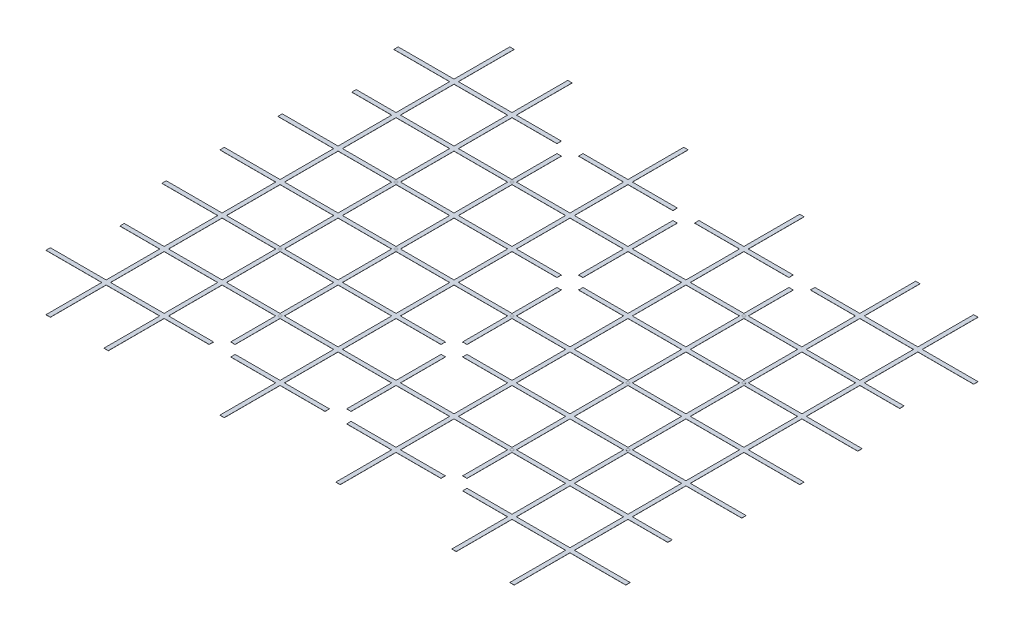
SolidWorks part; units mm, degrees
ref_plane "前视基准面" through (0, 0, 0) normal (0, 0, 1) x (1, 0, 0)
ref_plane "上视基准面" through (0, 0, 0) normal (0, 1, 0) x (1, 0, 0)
ref_plane "右视基准面" through (0, 0, 0) normal (1, 0, 0) x (0, 0, -1)
sketch "草图1" plane through (0, 0, 0) normal (0, 1, 0) x (1, 0, 0)
  line L1 (0, 0) -> (4000, 0)
  line L2 (0, 0) -> (0, 3200)
  line L3 (0, 3200) -> (4000, 3200)
  line L4 (4000, 0) -> (4000, 3200)
  dimension "D1" = 3200
  dimension "D2" = 4000
extrude "凸台-拉伸1" add sketch "草图1" along normal blind 1
sketch "草图2" plane through (0, 1, 0) normal (0, 1, 0) x (1, 0, 0)
  line L0 (0, 3200) -> (0, 0) construction
  line L1 (15, 15) -> (385, 15)
  line L2 (15, 15) -> (15, 385)
  line L3 (15, 385) -> (385, 385)
  line L4 (385, 15) -> (385, 385)
  line L5 (0, 0) -> (4000, 0) construction
  line L6 (200, 15) -> (200, 0) construction
  line L7 (415, 385) -> (785, 385)
  line L8 (415, 15) -> (415, 385)
  line L9 (415, 15) -> (785, 15)
  line L10 (785, 15) -> (785, 385)
  line L11 (815, 385) -> (1185, 385)
  line L12 (815, 15) -> (815, 385)
  line L13 (815, 15) -> (1185, 15)
  line L14 (1185, 15) -> (1185, 385)
  line L15 (1215, 385) -> (1585, 385)
  line L16 (1215, 15) -> (1215, 385)
  line L17 (1215, 15) -> (1585, 15)
  line L18 (1585, 15) -> (1585, 385)
  line L19 (1615, 385) -> (1985, 385)
  line L20 (1615, 15) -> (1615, 385)
  line L21 (1615, 15) -> (1985, 15)
  line L22 (1985, 15) -> (1985, 385)
  line L23 (2015, 385) -> (2385, 385)
  line L24 (2015, 15) -> (2015, 385)
  line L25 (2015, 15) -> (2385, 15)
  line L26 (2385, 15) -> (2385, 385)
  line L27 (2415, 385) -> (2785, 385)
  line L28 (2415, 15) -> (2415, 385)
  line L29 (2415, 15) -> (2785, 15)
  line L30 (2785, 15) -> (2785, 385)
  line L31 (2815, 385) -> (3185, 385)
  line L32 (2815, 15) -> (2815, 385)
  line L33 (2815, 15) -> (3185, 15)
  line L34 (3185, 15) -> (3185, 385)
  line L35 (3215, 385) -> (3585, 385)
  line L36 (3215, 15) -> (3215, 385)
  line L37 (3215, 15) -> (3585, 15)
  line L38 (3585, 15) -> (3585, 385)
  line L39 (3615, 385) -> (3985, 385)
  line L40 (3615, 15) -> (3615, 385)
  line L41 (3615, 15) -> (3985, 15)
  line L42 (3985, 15) -> (3985, 385)
  line L43 (415, 785) -> (785, 785)
  line L44 (415, 415) -> (415, 785)
  line L45 (415, 415) -> (785, 415)
  line L46 (785, 415) -> (785, 785)
  line L47 (815, 785) -> (1185, 785)
  line L48 (815, 415) -> (815, 785)
  line L49 (815, 415) -> (1185, 415)
  line L50 (1185, 415) -> (1185, 785)
  line L51 (1215, 785) -> (1585, 785)
  line L52 (1215, 415) -> (1215, 785)
  line L53 (1215, 415) -> (1585, 415)
  line L54 (1585, 415) -> (1585, 785)
  line L55 (1615, 785) -> (1985, 785)
  line L56 (1615, 415) -> (1615, 785)
  line L57 (1615, 415) -> (1985, 415)
  line L58 (1985, 415) -> (1985, 785)
  line L59 (2015, 785) -> (2385, 785)
  line L60 (2015, 415) -> (2015, 785)
  line L61 (2015, 415) -> (2385, 415)
  line L62 (2385, 415) -> (2385, 785)
  line L63 (2415, 785) -> (2785, 785)
  line L64 (2415, 415) -> (2415, 785)
  line L65 (2415, 415) -> (2785, 415)
  line L66 (2785, 415) -> (2785, 785)
  line L67 (2815, 785) -> (3185, 785)
  line L68 (2815, 415) -> (2815, 785)
  line L69 (2815, 415) -> (3185, 415)
  line L70 (3185, 415) -> (3185, 785)
  line L71 (3215, 785) -> (3585, 785)
  line L72 (3215, 415) -> (3215, 785)
  line L73 (3215, 415) -> (3585, 415)
  line L74 (3585, 415) -> (3585, 785)
  line L75 (3615, 785) -> (3985, 785)
  line L76 (3615, 415) -> (3615, 785)
  line L77 (3615, 415) -> (3985, 415)
  line L78 (3985, 415) -> (3985, 785)
  line L79 (415, 1185) -> (785, 1185)
  line L80 (415, 815) -> (415, 1185)
  line L81 (415, 815) -> (785, 815)
  line L82 (785, 815) -> (785, 1185)
  line L83 (815, 1185) -> (1185, 1185)
  line L84 (815, 815) -> (815, 1185)
  line L85 (815, 815) -> (1185, 815)
  line L86 (1185, 815) -> (1185, 1185)
  line L87 (1215, 1185) -> (1585, 1185)
  line L88 (1215, 815) -> (1215, 1185)
  line L89 (1215, 815) -> (1585, 815)
  line L90 (1585, 815) -> (1585, 1185)
  line L91 (1615, 1185) -> (1985, 1185)
  line L92 (1615, 815) -> (1615, 1185)
  line L93 (1615, 815) -> (1985, 815)
  line L94 (1985, 815) -> (1985, 1185)
  line L95 (2015, 1185) -> (2385, 1185)
  line L96 (2015, 815) -> (2015, 1185)
  line L97 (2015, 815) -> (2385, 815)
  line L98 (2385, 815) -> (2385, 1185)
  line L99 (2415, 1185) -> (2785, 1185)
  line L100 (2415, 815) -> (2415, 1185)
  line L101 (2415, 815) -> (2785, 815)
  line L102 (2785, 815) -> (2785, 1185)
  line L103 (2815, 1185) -> (3185, 1185)
  line L104 (2815, 815) -> (2815, 1185)
  line L105 (2815, 815) -> (3185, 815)
  line L106 (3185, 815) -> (3185, 1185)
  line L107 (3215, 1185) -> (3585, 1185)
  line L108 (3215, 815) -> (3215, 1185)
  line L109 (3215, 815) -> (3585, 815)
  line L110 (3585, 815) -> (3585, 1185)
  line L111 (3615, 1185) -> (3985, 1185)
  line L112 (3615, 815) -> (3615, 1185)
  line L113 (3615, 815) -> (3985, 815)
  line L114 (3985, 815) -> (3985, 1185)
  line L115 (415, 1585) -> (785, 1585)
  line L116 (415, 1215) -> (415, 1585)
  line L117 (415, 1215) -> (785, 1215)
  line L118 (785, 1215) -> (785, 1585)
  line L119 (815, 1585) -> (1185, 1585)
  line L120 (815, 1215) -> (815, 1585)
  line L121 (815, 1215) -> (1185, 1215)
  line L122 (1185, 1215) -> (1185, 1585)
  line L123 (1215, 1585) -> (1585, 1585)
  line L124 (1215, 1215) -> (1215, 1585)
  line L125 (1215, 1215) -> (1585, 1215)
  line L126 (1585, 1215) -> (1585, 1585)
  line L127 (1615, 1585) -> (1985, 1585)
  line L128 (1615, 1215) -> (1615, 1585)
  line L129 (1615, 1215) -> (1985, 1215)
  line L130 (1985, 1215) -> (1985, 1585)
  line L131 (2015, 1585) -> (2385, 1585)
  line L132 (2015, 1215) -> (2015, 1585)
  line L133 (2015, 1215) -> (2385, 1215)
  line L134 (2385, 1215) -> (2385, 1585)
  line L135 (2415, 1585) -> (2785, 1585)
  line L136 (2415, 1215) -> (2415, 1585)
  line L137 (2415, 1215) -> (2785, 1215)
  line L138 (2785, 1215) -> (2785, 1585)
  line L139 (2815, 1585) -> (3185, 1585)
  line L140 (2815, 1215) -> (2815, 1585)
  line L141 (2815, 1215) -> (3185, 1215)
  line L142 (3185, 1215) -> (3185, 1585)
  line L143 (3215, 1585) -> (3585, 1585)
  line L144 (3215, 1215) -> (3215, 1585)
  line L145 (3215, 1215) -> (3585, 1215)
  line L146 (3585, 1215) -> (3585, 1585)
  line L147 (3615, 1585) -> (3985, 1585)
  line L148 (3615, 1215) -> (3615, 1585)
  line L149 (3615, 1215) -> (3985, 1215)
  line L150 (3985, 1215) -> (3985, 1585)
  line L151 (415, 1985) -> (785, 1985)
  line L152 (415, 1615) -> (415, 1985)
  line L153 (415, 1615) -> (785, 1615)
  line L154 (785, 1615) -> (785, 1985)
  line L155 (815, 1985) -> (1185, 1985)
  line L156 (815, 1615) -> (815, 1985)
  line L157 (815, 1615) -> (1185, 1615)
  line L158 (1185, 1615) -> (1185, 1985)
  line L159 (1215, 1985) -> (1585, 1985)
  line L160 (1215, 1615) -> (1215, 1985)
  line L161 (1215, 1615) -> (1585, 1615)
  line L162 (1585, 1615) -> (1585, 1985)
  line L163 (1615, 1985) -> (1985, 1985)
  line L164 (1615, 1615) -> (1615, 1985)
  line L165 (1615, 1615) -> (1985, 1615)
  line L166 (1985, 1615) -> (1985, 1985)
  line L167 (2015, 1985) -> (2385, 1985)
  line L168 (2015, 1615) -> (2015, 1985)
  line L169 (2015, 1615) -> (2385, 1615)
  line L170 (2385, 1615) -> (2385, 1985)
  line L171 (2415, 1985) -> (2785, 1985)
  line L172 (2415, 1615) -> (2415, 1985)
  line L173 (2415, 1615) -> (2785, 1615)
  line L174 (2785, 1615) -> (2785, 1985)
  line L175 (2815, 1985) -> (3185, 1985)
  line L176 (2815, 1615) -> (2815, 1985)
  line L177 (2815, 1615) -> (3185, 1615)
  line L178 (3185, 1615) -> (3185, 1985)
  line L179 (3215, 1985) -> (3585, 1985)
  line L180 (3215, 1615) -> (3215, 1985)
  line L181 (3215, 1615) -> (3585, 1615)
  line L182 (3585, 1615) -> (3585, 1985)
  line L183 (3615, 1985) -> (3985, 1985)
  line L184 (3615, 1615) -> (3615, 1985)
  line L185 (3615, 1615) -> (3985, 1615)
  line L186 (3985, 1615) -> (3985, 1985)
  line L187 (415, 2385) -> (785, 2385)
  line L188 (415, 2015) -> (415, 2385)
  line L189 (415, 2015) -> (785, 2015)
  line L190 (785, 2015) -> (785, 2385)
  line L191 (815, 2385) -> (1185, 2385)
  line L192 (815, 2015) -> (815, 2385)
  line L193 (815, 2015) -> (1185, 2015)
  line L194 (1185, 2015) -> (1185, 2385)
  line L195 (1215, 2385) -> (1585, 2385)
  line L196 (1215, 2015) -> (1215, 2385)
  line L197 (1215, 2015) -> (1585, 2015)
  line L198 (1585, 2015) -> (1585, 2385)
  line L199 (1615, 2385) -> (1985, 2385)
  line L200 (1615, 2015) -> (1615, 2385)
  line L201 (1615, 2015) -> (1985, 2015)
  line L202 (1985, 2015) -> (1985, 2385)
  line L203 (2015, 2385) -> (2385, 2385)
  line L204 (2015, 2015) -> (2015, 2385)
  line L205 (2015, 2015) -> (2385, 2015)
  line L206 (2385, 2015) -> (2385, 2385)
  line L207 (2415, 2385) -> (2785, 2385)
  line L208 (2415, 2015) -> (2415, 2385)
  line L209 (2415, 2015) -> (2785, 2015)
  line L210 (2785, 2015) -> (2785, 2385)
  line L211 (2815, 2385) -> (3185, 2385)
  line L212 (2815, 2015) -> (2815, 2385)
  line L213 (2815, 2015) -> (3185, 2015)
  line L214 (3185, 2015) -> (3185, 2385)
  line L215 (3215, 2385) -> (3585, 2385)
  line L216 (3215, 2015) -> (3215, 2385)
  line L217 (3215, 2015) -> (3585, 2015)
  line L218 (3585, 2015) -> (3585, 2385)
  line L219 (3615, 2385) -> (3985, 2385)
  line L220 (3615, 2015) -> (3615, 2385)
  line L221 (3615, 2015) -> (3985, 2015)
  line L222 (3985, 2015) -> (3985, 2385)
  line L223 (415, 2785) -> (785, 2785)
  line L224 (415, 2415) -> (415, 2785)
  line L225 (415, 2415) -> (785, 2415)
  line L226 (785, 2415) -> (785, 2785)
  line L227 (815, 2785) -> (1185, 2785)
  line L228 (815, 2415) -> (815, 2785)
  line L229 (815, 2415) -> (1185, 2415)
  line L230 (1185, 2415) -> (1185, 2785)
  line L231 (1215, 2785) -> (1585, 2785)
  line L232 (1215, 2415) -> (1215, 2785)
  line L233 (1215, 2415) -> (1585, 2415)
  line L234 (1585, 2415) -> (1585, 2785)
  line L235 (1615, 2785) -> (1985, 2785)
  line L236 (1615, 2415) -> (1615, 2785)
  line L237 (1615, 2415) -> (1985, 2415)
  line L238 (1985, 2415) -> (1985, 2785)
  line L239 (2015, 2785) -> (2385, 2785)
  line L240 (2015, 2415) -> (2015, 2785)
  line L241 (2015, 2415) -> (2385, 2415)
  line L242 (2385, 2415) -> (2385, 2785)
  line L243 (2415, 2785) -> (2785, 2785)
  line L244 (2415, 2415) -> (2415, 2785)
  line L245 (2415, 2415) -> (2785, 2415)
  line L246 (2785, 2415) -> (2785, 2785)
  line L247 (2815, 2785) -> (3185, 2785)
  line L248 (2815, 2415) -> (2815, 2785)
  line L249 (2815, 2415) -> (3185, 2415)
  line L250 (3185, 2415) -> (3185, 2785)
  line L251 (3215, 2785) -> (3585, 2785)
  line L252 (3215, 2415) -> (3215, 2785)
  line L253 (3215, 2415) -> (3585, 2415)
  line L254 (3585, 2415) -> (3585, 2785)
  line L255 (3615, 2785) -> (3985, 2785)
  line L256 (3615, 2415) -> (3615, 2785)
  line L257 (3615, 2415) -> (3985, 2415)
  line L258 (3985, 2415) -> (3985, 2785)
  line L259 (415, 3185) -> (785, 3185)
  line L260 (415, 2815) -> (415, 3185)
  line L261 (415, 2815) -> (785, 2815)
  line L262 (785, 2815) -> (785, 3185)
  line L263 (815, 3185) -> (1185, 3185)
  line L264 (815, 2815) -> (815, 3185)
  line L265 (815, 2815) -> (1185, 2815)
  line L266 (1185, 2815) -> (1185, 3185)
  line L267 (1215, 3185) -> (1585, 3185)
  line L268 (1215, 2815) -> (1215, 3185)
  line L269 (1215, 2815) -> (1585, 2815)
  line L270 (1585, 2815) -> (1585, 3185)
  line L271 (1615, 3185) -> (1985, 3185)
  line L272 (1615, 2815) -> (1615, 3185)
  line L273 (1615, 2815) -> (1985, 2815)
  line L274 (1985, 2815) -> (1985, 3185)
  line L275 (2015, 3185) -> (2385, 3185)
  line L276 (2015, 2815) -> (2015, 3185)
  line L277 (2015, 2815) -> (2385, 2815)
  line L278 (2385, 2815) -> (2385, 3185)
  line L279 (2415, 3185) -> (2785, 3185)
  line L280 (2415, 2815) -> (2415, 3185)
  line L281 (2415, 2815) -> (2785, 2815)
  line L282 (2785, 2815) -> (2785, 3185)
  line L283 (2815, 3185) -> (3185, 3185)
  line L284 (2815, 2815) -> (2815, 3185)
  line L285 (2815, 2815) -> (3185, 2815)
  line L286 (3185, 2815) -> (3185, 3185)
  line L287 (3215, 3185) -> (3585, 3185)
  line L288 (3215, 2815) -> (3215, 3185)
  line L289 (3215, 2815) -> (3585, 2815)
  line L290 (3585, 2815) -> (3585, 3185)
  line L291 (3615, 3185) -> (3985, 3185)
  line L292 (3615, 2815) -> (3615, 3185)
  line L293 (3615, 2815) -> (3985, 2815)
  line L294 (3985, 2815) -> (3985, 3185)
  line L295 (15, 785) -> (385, 785)
  line L296 (15, 415) -> (15, 785)
  line L297 (15, 415) -> (385, 415)
  line L298 (385, 415) -> (385, 785)
  line L299 (15, 1185) -> (385, 1185)
  line L300 (15, 815) -> (15, 1185)
  line L301 (15, 815) -> (385, 815)
  line L302 (385, 815) -> (385, 1185)
  line L303 (15, 1585) -> (385, 1585)
  line L304 (15, 1215) -> (15, 1585)
  line L305 (15, 1215) -> (385, 1215)
  line L306 (385, 1215) -> (385, 1585)
  line L307 (15, 1985) -> (385, 1985)
  line L308 (15, 1615) -> (15, 1985)
  line L309 (15, 1615) -> (385, 1615)
  line L310 (385, 1615) -> (385, 1985)
  line L311 (15, 2385) -> (385, 2385)
  line L312 (15, 2015) -> (15, 2385)
  line L313 (15, 2015) -> (385, 2015)
  line L314 (385, 2015) -> (385, 2385)
  line L315 (15, 2785) -> (385, 2785)
  line L316 (15, 2415) -> (15, 2785)
  line L317 (15, 2415) -> (385, 2415)
  line L318 (385, 2415) -> (385, 2785)
  line L319 (15, 3185) -> (385, 3185)
  line L320 (15, 2815) -> (15, 3185)
  line L321 (15, 2815) -> (385, 2815)
  line L322 (385, 2815) -> (385, 3185)
  dimension "D1" = 15
  dimension "D2" = 15
  dimension "D3" = 200
  dimension "D4" = 10
  dimension "D5" = 8
extrude "切除-拉伸2" cut sketch "草图2" against normal through all
sketch "草图4" plane through (0, 1, 0) normal (0, 1, 0) x (1, 0, 0)
  line L1 (0, 3200) -> (385, 3200)
  line L2 (0, 3200) -> (0, 2815)
  line L3 (0, 2815) -> (385, 2815)
  line L4 (385, 3200) -> (385, 2815)
  line L5 (4000, 3200) -> (3615, 3200)
  line L6 (4000, 3200) -> (4000, 2815)
  line L7 (4000, 2815) -> (3615, 2815)
  line L8 (3615, 3200) -> (3615, 2815)
  line L9 (4000, 0) -> (3615, 0)
  line L10 (4000, 0) -> (4000, 385)
  line L11 (4000, 385) -> (3615, 385)
  line L12 (3615, 0) -> (3615, 385)
  line L13 (0, 0) -> (385, 0)
  line L14 (0, 0) -> (0, 385)
  line L15 (0, 385) -> (385, 385)
  line L16 (385, 0) -> (385, 385)
extrude "切除-拉伸4" cut sketch "草图4" against normal through all
sketch "草图5" plane through (0, 1, 0) normal (0, 1, 0) x (1, 0, 0)
  line L0 (385, 0) -> (3615, 0) construction
  line L1 (415, 15) -> (785, 15)
  line L2 (415, 15) -> (415, 0)
  line L3 (415, 0) -> (785, 0)
  line L4 (785, 15) -> (785, 0)
  line L5 (815, 15) -> (815, 0)
  line L6 (815, 15) -> (1185, 15)
  line L7 (815, 0) -> (1185, 0)
  line L8 (1185, 15) -> (1185, 0)
  line L9 (1215, 15) -> (1215, 0)
  line L10 (1215, 15) -> (1585, 15)
  line L11 (1215, 0) -> (1585, 0)
  line L12 (1585, 15) -> (1585, 0)
  line L13 (1615, 15) -> (1615, 0)
  line L14 (1615, 15) -> (1985, 15)
  line L15 (1615, 0) -> (1985, 0)
  line L16 (1985, 15) -> (1985, 0)
  line L17 (2015, 15) -> (2015, 0)
  line L18 (2015, 15) -> (2385, 15)
  line L19 (2015, 0) -> (2385, 0)
  line L20 (2385, 15) -> (2385, 0)
  line L21 (2415, 15) -> (2415, 0)
  line L22 (2415, 15) -> (2785, 15)
  line L23 (2415, 0) -> (2785, 0)
  line L24 (2785, 15) -> (2785, 0)
  line L25 (2815, 15) -> (2815, 0)
  line L26 (2815, 15) -> (3185, 15)
  line L27 (2815, 0) -> (3185, 0)
  line L28 (3185, 15) -> (3185, 0)
  line L29 (3215, 15) -> (3215, 0)
  line L30 (3215, 15) -> (3585, 15)
  line L31 (3215, 0) -> (3585, 0)
  line L32 (3585, 15) -> (3585, 0)
  line L33 (815, 3200) -> (815, 3185)
  line L34 (815, 3200) -> (1185, 3200)
  line L35 (815, 3185) -> (1185, 3185)
  line L36 (1185, 3200) -> (1185, 3185)
  line L37 (1215, 3200) -> (1215, 3185)
  line L38 (1215, 3200) -> (1585, 3200)
  line L39 (1215, 3185) -> (1585, 3185)
  line L40 (1585, 3200) -> (1585, 3185)
  line L41 (1615, 3200) -> (1615, 3185)
  line L42 (1615, 3200) -> (1985, 3200)
  line L43 (1615, 3185) -> (1985, 3185)
  line L44 (1985, 3200) -> (1985, 3185)
  line L45 (2015, 3200) -> (2015, 3185)
  line L46 (2015, 3200) -> (2385, 3200)
  line L47 (2015, 3185) -> (2385, 3185)
  line L48 (2385, 3200) -> (2385, 3185)
  line L49 (2415, 3200) -> (2415, 3185)
  line L50 (2415, 3200) -> (2785, 3200)
  line L51 (2415, 3185) -> (2785, 3185)
  line L52 (2785, 3200) -> (2785, 3185)
  line L53 (2815, 3200) -> (2815, 3185)
  line L54 (2815, 3200) -> (3185, 3200)
  line L55 (2815, 3185) -> (3185, 3185)
  line L56 (3185, 3200) -> (3185, 3185)
  line L57 (3215, 3200) -> (3215, 3185)
  line L58 (3215, 3200) -> (3585, 3200)
  line L59 (3215, 3185) -> (3585, 3185)
  line L60 (3585, 3200) -> (3585, 3185)
  line L61 (415, 3200) -> (415, 3185)
  line L62 (415, 3200) -> (785, 3200)
  line L63 (415, 3185) -> (785, 3185)
  line L64 (785, 3200) -> (785, 3185)
  line L65 (0, 2815) -> (0, 385) construction
  line L66 (15, 415) -> (0, 415)
  line L67 (15, 415) -> (15, 785)
  line L68 (15, 785) -> (0, 785)
  line L69 (0, 415) -> (0, 785)
  line L70 (385, 785) -> (15, 785) construction
  line L71 (4000, 785) -> (3985, 785)
  line L72 (3985, 415) -> (3985, 785)
  line L73 (4000, 415) -> (4000, 785)
  line L74 (4000, 415) -> (3985, 415)
  line L75 (4000, 1185) -> (3985, 1185)
  line L76 (3985, 815) -> (3985, 1185)
  line L77 (4000, 815) -> (4000, 1185)
  line L78 (4000, 815) -> (3985, 815)
  line L79 (4000, 1585) -> (3985, 1585)
  line L80 (3985, 1215) -> (3985, 1585)
  line L81 (4000, 1215) -> (4000, 1585)
  line L82 (4000, 1215) -> (3985, 1215)
  line L83 (4000, 1985) -> (3985, 1985)
  line L84 (3985, 1615) -> (3985, 1985)
  line L85 (4000, 1615) -> (4000, 1985)
  line L86 (4000, 1615) -> (3985, 1615)
  line L87 (4000, 2385) -> (3985, 2385)
  line L88 (3985, 2015) -> (3985, 2385)
  line L89 (4000, 2015) -> (4000, 2385)
  line L90 (4000, 2015) -> (3985, 2015)
  line L91 (4000, 2785) -> (3985, 2785)
  line L92 (3985, 2415) -> (3985, 2785)
  line L93 (4000, 2415) -> (4000, 2785)
  line L94 (4000, 2415) -> (3985, 2415)
  line L95 (15, 1185) -> (0, 1185)
  line L96 (0, 815) -> (0, 1185)
  line L97 (15, 815) -> (15, 1185)
  line L98 (15, 815) -> (0, 815)
  line L99 (15, 1585) -> (0, 1585)
  line L100 (0, 1215) -> (0, 1585)
  line L101 (15, 1215) -> (15, 1585)
  line L102 (15, 1215) -> (0, 1215)
  line L103 (15, 1985) -> (0, 1985)
  line L104 (0, 1615) -> (0, 1985)
  line L105 (15, 1615) -> (15, 1985)
  line L106 (15, 1615) -> (0, 1615)
  line L107 (15, 2385) -> (0, 2385)
  line L108 (0, 2015) -> (0, 2385)
  line L109 (15, 2015) -> (15, 2385)
  line L110 (15, 2015) -> (0, 2015)
  line L111 (15, 2785) -> (0, 2785)
  line L112 (0, 2415) -> (0, 2785)
  line L113 (15, 2415) -> (15, 2785)
  line L114 (15, 2415) -> (0, 2415)
  dimension "D1" = 8
  dimension "D2" = 2
  dimension "D3" = 2
  dimension "D4" = 6
extrude "切除-拉伸5" cut sketch "草图5" against normal through all
sketch "草图6" plane through (0, 1, 0) normal (0, 1, 0) x (1, 0, 0)
  line L0 (385, 2385) -> (0, 2385) construction
  line L1 (0, 2415) -> (110, 2415)
  line L2 (0, 2415) -> (0, 2385)
  line L3 (0, 2385) -> (110, 2385)
  line L4 (110, 2415) -> (110, 2385)
  line L5 (0, 815) -> (385, 815) construction
  line L6 (0, 785) -> (110, 785)
  line L7 (0, 785) -> (0, 815)
  line L8 (0, 815) -> (110, 815)
  line L9 (110, 785) -> (110, 815)
  line L10 (4000, 785) -> (3615, 785) construction
  line L11 (4000, 815) -> (3890, 815)
  line L12 (4000, 815) -> (4000, 785)
  line L13 (4000, 785) -> (3890, 785)
  line L14 (3890, 815) -> (3890, 785)
  line L15 (4000, 2385) -> (3615, 2385) construction
  line L16 (4000, 2415) -> (3890, 2415)
  line L17 (4000, 2415) -> (4000, 2385)
  line L18 (4000, 2385) -> (3890, 2385)
  line L19 (3890, 2415) -> (3890, 2385)
  line L20 (1200, 3200) -> (1200, 2800) construction
  line L21 (1215, 3200) -> (1185, 3200) construction
  line L23 (1125, 3200) -> (1275, 3200)
  line L24 (1125, 3200) -> (1125, 2800)
  line L25 (1125, 2800) -> (1275, 2800) construction
  line L26 (1275, 3200) -> (1275, 2800)
  line L27 (2000, 3200) -> (2000, 2800) construction
  line L28 (1925, 3200) -> (2075, 3200)
  line L29 (1925, 3200) -> (1925, 2800)
  line L30 (1925, 2800) -> (2075, 2800) construction
  line L31 (2075, 3200) -> (2075, 2800)
  line L32 (2015, 3200) -> (1985, 3200) construction
  line L33 (2800, 3200) -> (2800, 2800) construction
  line L34 (2725, 3200) -> (2875, 3200)
  line L35 (2725, 3200) -> (2725, 2800)
  line L36 (2725, 2800) -> (2875, 2800) construction
  line L37 (2875, 3200) -> (2875, 2800)
  line L38 (2815, 3200) -> (2785, 3200) construction
  line L39 (0, 2015) -> (0, 1985) construction
  line L40 (0, 1600) -> (4000, 1600) construction
  line L41 (0, 1615) -> (0, 1585) construction
  line L42 (4000, 1585) -> (4000, 1615) construction
  line L43 (2875, 0) -> (2875, 400)
  line L44 (2725, 0) -> (2725, 400)
  line L45 (2725, 0) -> (2875, 0)
  line L46 (2075, 0) -> (2075, 400)
  line L47 (1925, 0) -> (1925, 400)
  line L48 (1925, 0) -> (2075, 0)
  line L49 (1275, 0) -> (1275, 400)
  line L50 (1125, 0) -> (1125, 400)
  line L51 (1125, 0) -> (1275, 0)
  arc A0 (1125, 2800) -> (1275, 2800) centre (1200, 2800) ccw
  arc A1 (1925, 2800) -> (2075, 2800) centre (2000, 2800) ccw
  arc A2 (2725, 2800) -> (2875, 2800) centre (2800, 2800) ccw
  circle A3 centre (2000, 2000) radius 75
  circle A4 centre (2000, 1200) radius 75
  arc A5 (2725, 400) -> (2875, 400) centre (2800, 400) cw
  arc A6 (1925, 400) -> (2075, 400) centre (2000, 400) cw
  arc A7 (1125, 400) -> (1275, 400) centre (1200, 400) cw
  dimension "D4" = 1200
  dimension "D5" = 2000
  dimension "D6" = 150
  dimension "D1" = 110
  dimension "D2" = 400
  dimension "D3" = 150
extrude "切除-拉伸6" cut sketch "草图6" against normal through all
sketch "草图7" plane through (0, 1, 0) normal (0, 1, 0) x (1, 0, 0)
  line L0 (815, 2415) -> (1185, 2415) construction
  line L1 (1185, 2015) -> (1185, 2385) construction
  line L2 (415, 2015) -> (785, 2015) construction
  line L3 (785, 2015) -> (785, 2385) construction
  line L4 (1185, 1615) -> (1185, 1985) construction
  line L5 (815, 1615) -> (1185, 1615) construction
  line L6 (1185, 815) -> (1185, 1185) construction
  line L7 (815, 815) -> (1185, 815) construction
  line L8 (415, 1215) -> (785, 1215) construction
  line L9 (785, 1215) -> (785, 1585) construction
  line L10 (1985, 1615) -> (1985, 1926.5153) construction
  line L11 (1615, 1615) -> (1985, 1615) construction
  line L12 (2000, 1716.566) -> (2000, 1600) construction
  circle A0 centre (1200, 2400) radius 10
  circle A1 centre (1200, 1600) radius 10
  circle A2 centre (1200, 800) radius 10
  circle A3 centre (800, 2000) radius 10
  circle A4 centre (800, 1200) radius 10
  circle A5 centre (2000, 1600) radius 10
  circle A6 centre (2800, 800) radius 10
  circle A7 centre (3200, 1200) radius 10
  circle A8 centre (2800, 1600) radius 10
  circle A9 centre (3200, 2000) radius 10
  circle A10 centre (2800, 2400) radius 10
  dimension "D1" = 20
  dimension "D5" = 15
  dimension "D6" = 15
  dimension "D8" = 15
  dimension "D9" = 15
  dimension "D10" = 15
  dimension "D12" = 15
  dimension "D13" = 15
  dimension "D2" = 15
  dimension "D3" = 15
  dimension "D4" = 15
  dimension "D7" = 15
  dimension "D11" = 15
extrude "凸台-拉伸2" add sketch "草图7" along normal blind 0.1
